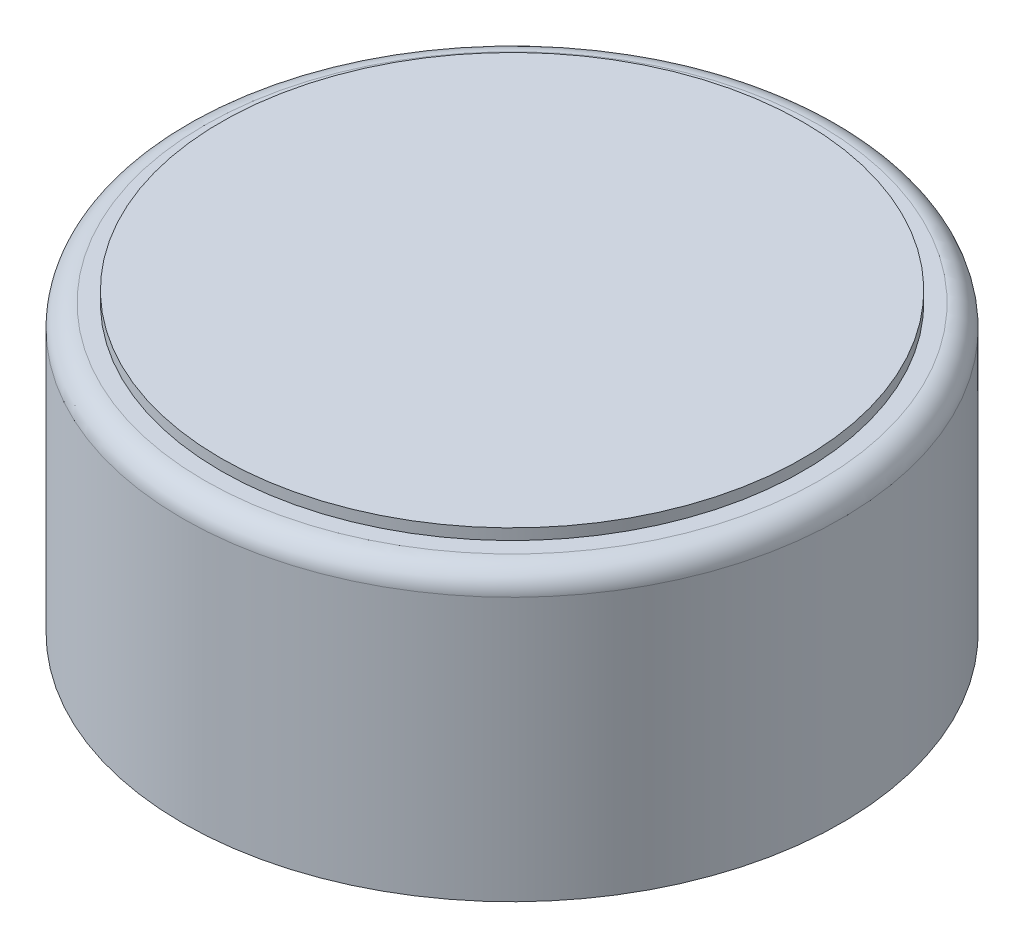
SolidWorks part; units mm, degrees
ref_plane "Front Plane" through (0, 0, 0) normal (0, 0, 1) x (1, 0, 0)
ref_plane "Top Plane" through (0, 0, 0) normal (0, 1, 0) x (1, 0, 0)
ref_plane "Right Plane" through (0, 0, 0) normal (1, 0, 0) x (0, 0, -1)
sketch "Sketch1" plane through (0, 0, 0) normal (0, 1, 0) x (1, 0, 0)
  circle A0 centre (0, 0) radius 3
  dimension "D1" = 6
extrude "Boss-Extrude1" add sketch "Sketch1" along normal blind 2.6
fillet "Fillet1" radius 0.2 1 edges at (0, 2.6, 3)
sketch "Sketch2" plane through (0, 2.6, 0) normal (0, 1, 0) x (1, 0, 0)
  circle A0 centre (0, 0) radius 2.65
  dimension "D1" = 5.3
extrude "Boss-Extrude2" add sketch "Sketch2" along normal blind 0.1
sketch "Sketch3" plane through (0, 0, 0) normal (0, -1, 0) x (1, 0, 0)
  line L0 (0, 0) -> (-1.27, 0) construction
  line L1 (-1.27, -1.27) -> (-1.27, 1.27) construction
  circle A0 centre (-1.27, 1.27) radius 0.2
  circle A1 centre (-1.27, -1.27) radius 0.25
  dimension "D1" = 0.4
  dimension "D2" = 0.5
  dimension "D3" = 2.54
  dimension "D4" = 1.27
extrude "Boss-Extrude3" add sketch "Sketch3" along normal blind 1
